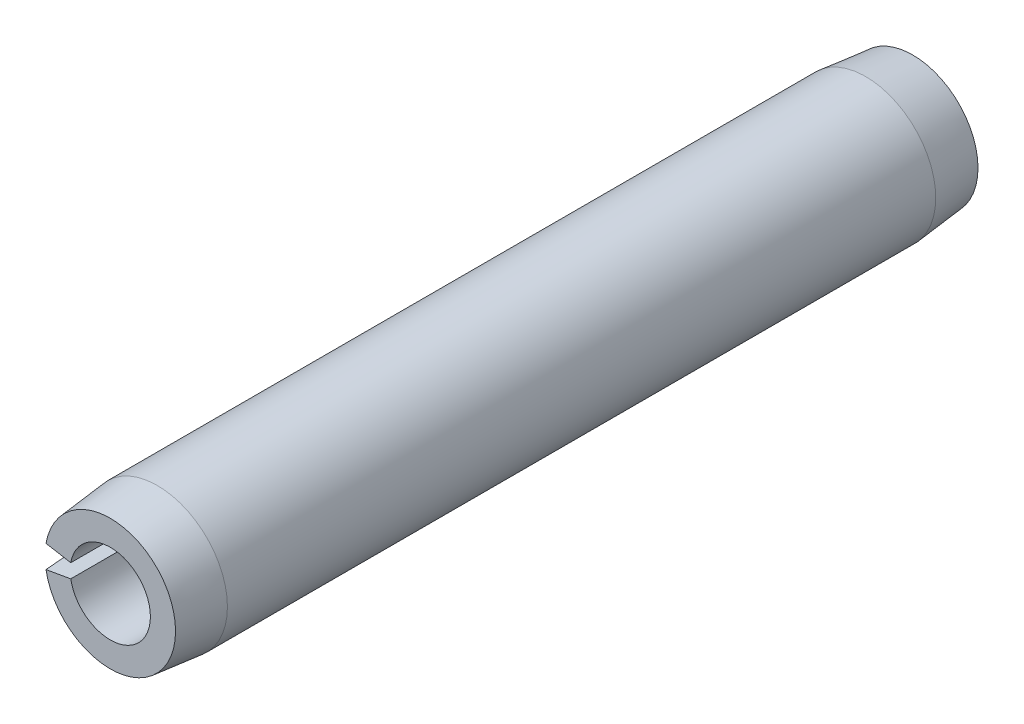
SolidWorks part; units mm, degrees
ref_plane "Front Plane" through (0, 0, 0) normal (0, 0, 1) x (1, 0, 0)
ref_plane "Top Plane" through (0, 0, 0) normal (0, 1, 0) x (1, 0, 0)
ref_plane "Right Plane" through (0, 0, 0) normal (1, 0, 0) x (0, 0, -1)
sketch "Sketch1" plane through (0, 0, 0) normal (0, 0, 1) x (1, 0, 0)
  line L0 (0.9525, 0) -> (1.6637, 0) construction
  line L1 (-1.6384, 0.2889) -> (-0.938, 0.1654)
  line L2 (-0.938, -0.1654) -> (-1.6384, -0.2889)
  arc A0 (-1.6384, -0.2889) -> (-1.6384, 0.2889) centre (0, 0) ccw
  arc A1 (-0.938, -0.1654) -> (-0.938, 0.1654) centre (0, 0) ccw
  dimension "OD" = 3.3274
  dimension "Wall thickness" = 0.7112
  dimension "D3" = 20
extrude "Extrude1" add sketch "Sketch1" along normal mid plane 19.05
sketch "Sketch2" plane through (0, 0, 0) normal (1, 0, 0) x (0, 0, -1)
  line L0 (0, -1.6637) -> (0, 1.6637) construction
  line L1 (9.525, 0) -> (-9.525, 0) construction
  line L2 (9.525, -0.9525) -> (9.525, 0.9525) construction
  line L3 (9.525, 1.6637) -> (-9.525, 1.6637) construction
  line L4 (9.525, 1.6637) -> (9.525, 1.5494)
  line L5 (9.525, 1.5494) -> (8.4074, 1.6637)
  line L6 (8.4074, 1.6637) -> (9.525, 1.6637)
  line L7 (9.525, -1.6637) -> (9.525, 1.6637) construction
  line L8 (-8.4074, 1.6637) -> (-9.525, 1.6637)
  line L9 (-9.525, 1.5494) -> (-8.4074, 1.6637)
  line L10 (-9.525, 1.6637) -> (-9.525, 1.5494)
  line L11 (8.4074, -1.6637) -> (9.525, -1.6637) construction
  line L12 (9.525, -1.5494) -> (8.4074, -1.6637) construction
  line L13 (9.525, -1.6637) -> (9.525, -1.5494) construction
  dimension "B" = 3.0988
  dimension "Chamfer max" = 1.1176
revolve "Cut-Revolve1" cut sketch "Sketch2" angle 360 about L1
sketch "Sketch3" plane through (0, 0, 0) normal (0, 0, 1) x (1, 0, 0)
  line L0 (0.9525, 0) -> (1.6637, 0) construction
  line L1 (0.9525, 0) -> (1.6637, 0)
  circle A0 centre (0, 0) radius 1.6637
  circle A1 centre (0, 0) radius 0.9525
  arc A2 (-1.6384, -0.2889) -> (-1.6384, 0.2889) centre (0, 0) ccw construction
  arc A3 (-0.938, -0.1654) -> (-0.938, 0.1654) centre (0, 0) ccw construction
